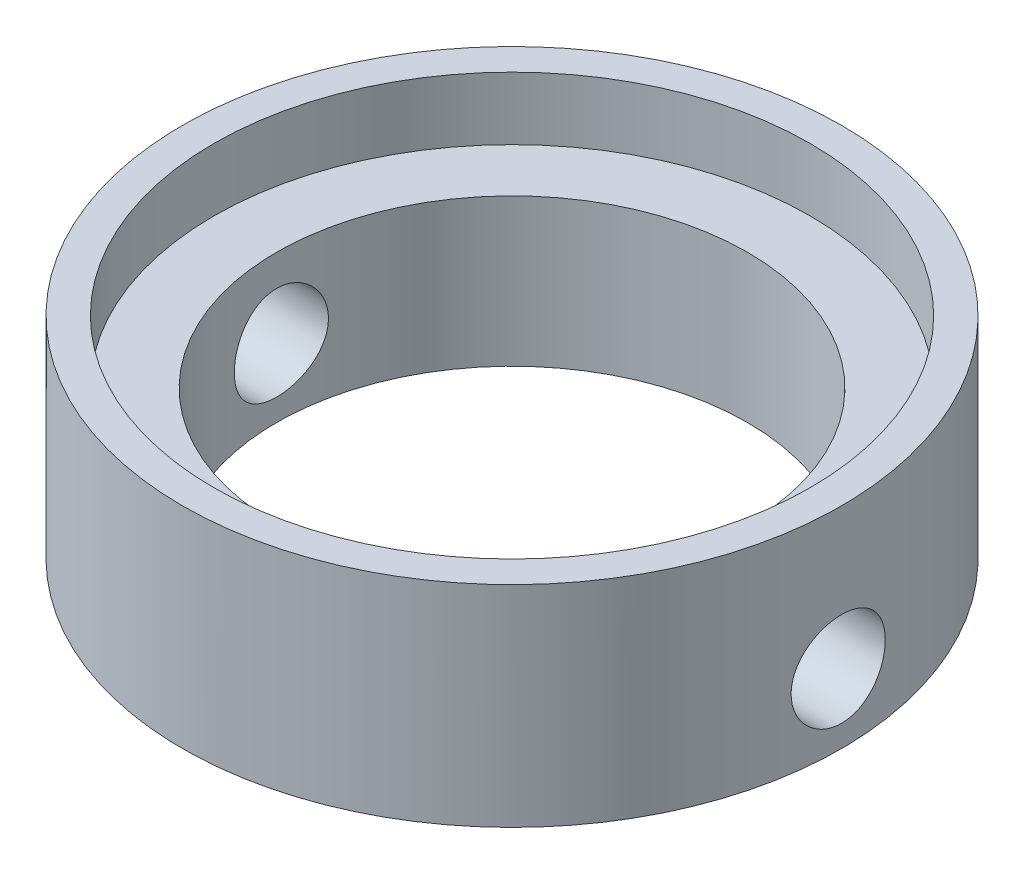
SolidWorks part; units mm, degrees
ref_plane "Piano frontale" through (0, 0, 0) normal (0, 0, 1) x (1, 0, 0)
ref_plane "Piano superiore" through (0, 0, 0) normal (0, 1, 0) x (1, 0, 0)
ref_plane "Piano destro" through (0, 0, 0) normal (1, 0, 0) x (0, 0, -1)
sketch "Schizzo1" plane through (0, 0, 0) normal (0, 1, 0) x (1, 0, 0)
  circle A0 centre (0, 0) radius 10.5
  dimension "D1" = 21
extrude "Estrusione-Estrusione1" add sketch "Schizzo1" along normal blind 7
sketch "Schizzo2" plane through (0, 7, 0) normal (0, 1, 0) x (1, 0, 0)
  circle A0 centre (0, 0) radius 9.5
  dimension "D1" = 19
extrude "Taglio-Estrusione1" cut sketch "Schizzo2" against normal blind 2
sketch "Schizzo3" plane through (0, 5, 0) normal (0, 1, 0) x (1, 0, 0)
  circle A0 centre (0, 0) radius 7.5
  dimension "D1" = 15
extrude "Taglio-Estrusione2" cut sketch "Schizzo3" against normal through all
sketch "Schizzo4" plane through (0, 0, 0) normal (1, 0, 0) x (0, 0, -1)
  circle A0 centre (0, 2.5) radius 1.5
  dimension "D1" = 3
  dimension "D2" = 2.5
extrude "Taglio-Estrusione3" cut sketch "Schizzo4" against normal through all and the other way through all
sketch "Schizzo5" plane through (0, 0, 0) normal (0, -1, 0) x (1, 0, 0)
  line L0 (0, 10.5) -> (0, -10.5) construction
  circle A0 centre (0, 0) radius 10.5 construction
sketch "Schizzo6" plane through (0, 0, 0) normal (0, -1, 0) x (1, 0, 0)
  circle A0 centre (0, 0) radius 10.5
extrude "Taglio-Estrusione4" cut sketch "Schizzo6" against normal blind 0.3
